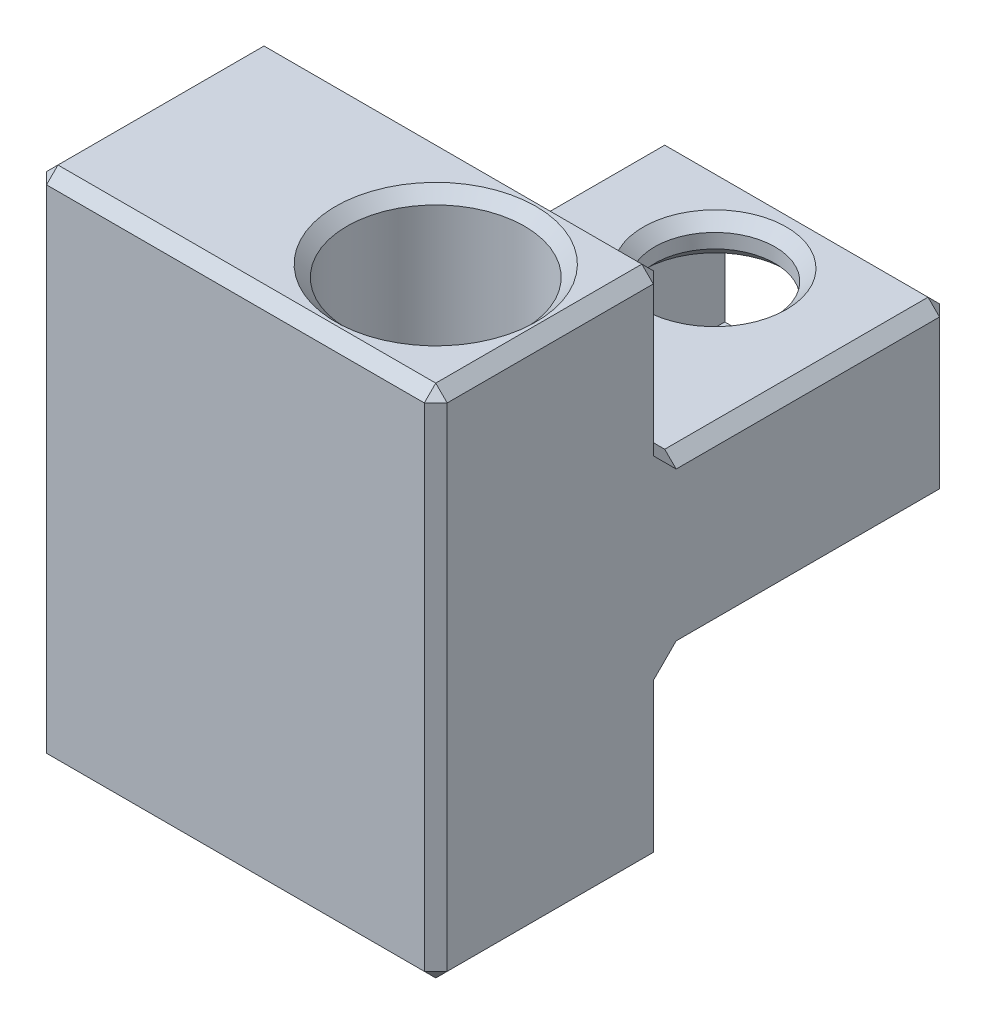
SolidWorks part; units mm, degrees
material "ABS"
ref_plane "Front Plane" through (0, 0, 0) normal (0, 0, 1) x (1, 0, 0)
ref_plane "Top Plane" through (0, 0, 0) normal (0, 1, 0) x (1, 0, 0)
ref_plane "Right Plane" through (0, 0, 0) normal (1, 0, 0) x (0, 0, -1)
sketch "Sketch1" plane through (0, 0, 0) normal (0, 1, 0) x (1, 0, 0)
  line L1 (0, 0) -> (35, 0)
  line L2 (0, 0) -> (0, 20)
  line L3 (0, 20) -> (35, 20)
  line L4 (35, 0) -> (35, 20)
  dimension "D1" = 20
  dimension "D2" = 35
extrude "Boss-Extrude1" add sketch "Sketch1" along normal blind 45
sketch "Sketch2" plane through (0, 45, 0) normal (0, 1, 0) x (1, 0, 0)
  line L0 (15, 0) -> (35, 20) construction
  line L1 (35, 20) -> (0, 20) construction
  line L4 (35, 0) -> (35, 20) construction
  line L5 (0, 0) -> (35, 0) construction
  circle A0 centre (25, 10) radius 7.75
  point P5 (0, 0)
  point P6 (0, 0)
  point P10 (0, 0)
  point P11 (0, 0)
  point P14 (0, 0)
  dimension "D1" = 45
extrude "Cut-Extrude1" cut sketch "Sketch2" against normal through all
sketch "Sketch10" plane through (0, 0, 0) normal (-1, 0, 0) x (0, 0, 1)
  line L0 (-10, 0) -> (-10, 45) construction
  line L1 (0, 0) -> (-20, 0) construction
  line L2 (-20, 45) -> (0, 45) construction
  circle A0 centre (-10, 37.6875) radius 4.25
  circle A1 centre (-10, 7.3125) radius 4.25
  dimension "D1" = 8.5
  dimension "D2" = 7.3125
  dimension "D3" = 7.3125
extrude "Cut-Extrude6" cut sketch "Sketch10" against normal blind 10
sketch "Sketch4" plane through (0, 0, -20) normal (0, 0, -1) x (-1, 0, 0)
  line L1 (-10, 15) -> (-35, 15)
  line L2 (-10, 15) -> (-10, 30)
  line L3 (-10, 30) -> (-35, 30)
  line L4 (-35, 15) -> (-35, 30)
  line L6 (-35, 45) -> (-35, 0) construction
  point P8 (0, 0)
  point P9 (0, 0)
  point P11 (-35, 22.5)
  point P12 (-35, 22.5)
  dimension "D1" = 15
  dimension "D2" = 25
extrude "Boss-Extrude2" add sketch "Sketch4" along normal blind 25
sketch "Sketch5" plane through (0, 30, 0) normal (0, 1, 0) x (1, 0, 0)
  line L0 (10, 45) -> (35, 45) construction
  line L1 (29.75, 45) -> (15.25, 45)
  line L2 (29.75, 45) -> (29.75, 28.75)
  line L3 (29.75, 28.75) -> (15.25, 28.75)
  line L4 (15.25, 45) -> (15.25, 28.75)
  line L6 (29.75, 45) -> (35, 45) construction
  line L7 (15.25, 45) -> (10, 45) construction
  point P6 (0, 0)
  dimension "D1" = 14.5
  dimension "D2" = 16.25
extrude "Cut-Extrude3" cut sketch "Sketch5" against normal through all
sketch "Sketch6" plane through (15.25, 0, 0) normal (1, 0, 0) x (0, 0, -1)
  line L0 (28.75, 15) -> (28.75, 30) construction
  line L1 (45, 30) -> (28.75, 30)
  line L2 (45, 30) -> (45, 26.75)
  line L3 (45, 26.75) -> (28.75, 26.75)
  line L4 (28.75, 30) -> (28.75, 26.75)
  line L6 (45, 15) -> (28.75, 15)
  line L7 (45, 15) -> (45, 18.25)
  line L8 (45, 18.25) -> (28.75, 18.25)
  line L9 (28.75, 15) -> (28.75, 18.25)
  dimension "D1" = 3.25
extrude "Boss-Extrude3" add sketch "Sketch6" along normal up to next
sketch "Sketch7" plane through (0, 18.25, 0) normal (0, 1, 0) x (1, 0, 0)
  line L0 (15.25, 36.875) -> (29.75, 36.875) construction
  line L1 (15.25, 45) -> (15.25, 28.75) construction
  line L2 (29.75, 45) -> (29.75, 28.75) construction
  circle A0 centre (22.5, 36.875) radius 5.25
  point P9 (22.5, 36.875)
  point P10 (0, 0)
extrude "Cut-Extrude4" cut sketch "Sketch7" against normal through all both and the other way through all
chamfer "Chamfer1" distance 1 angle 45 30 edges at (27.75, 30, -36.875) (25, 0, -2.25) (25, 45, -2.25) (22.5, 26.75, -31.625) (22.5, 18.25, -42.125) (17.25, 15, -36.875) (22.5, 15, -20) (35, 7.5, -20) (35, 37.5, -20) (22.5, 30, -20) (22.5, 30, -45) (35, 30, -32.5) (35, 22.5, -45) (35, 15, -32.5) (35, 0, -10) (17.5, 0, -20) (0, 22.5, -20) (0, 0, -10) (0, 22.5, 0) (17.5, 0, 0) (35, 22.5, 0) (17.5, 45, -20) (35, 45, -10) (17.5, 45, 0) (0, 45, -10) (10, 30, -32.5) (22.5, 15, -45) (10, 22.5, -20) (0, 7.3125, -5.75) (0, 37.6875, -5.75)
